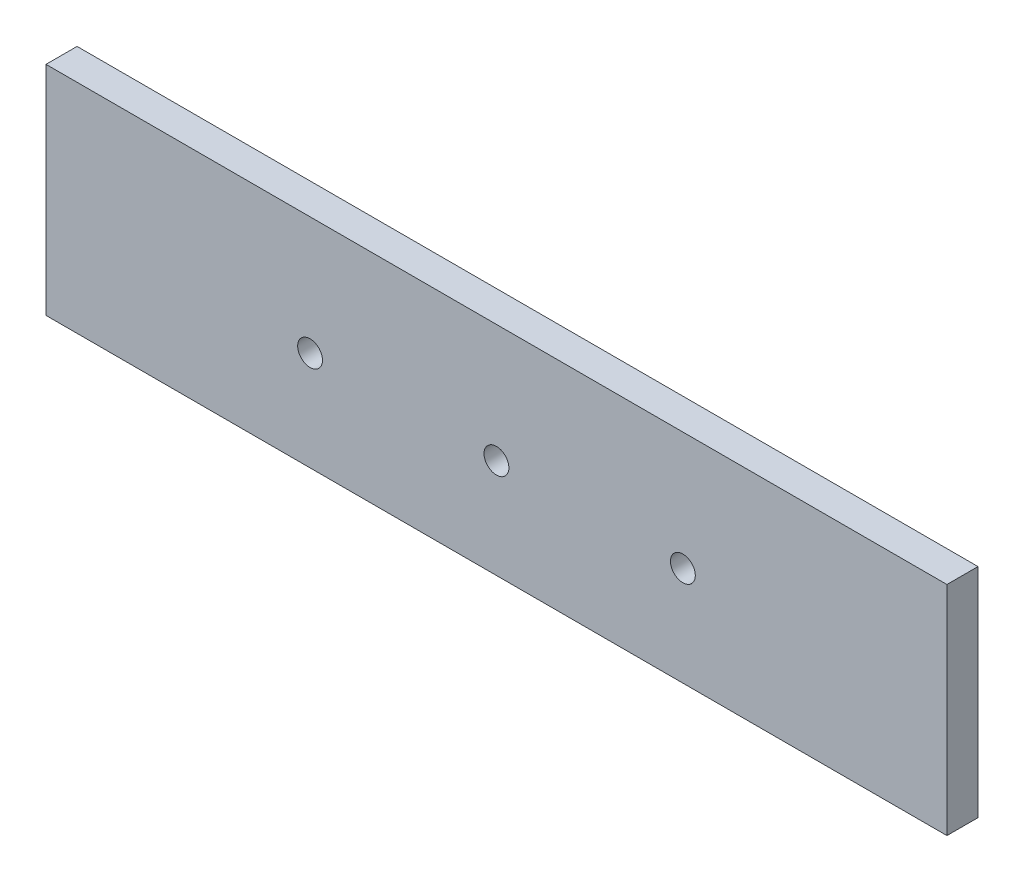
SolidWorks part; units mm, degrees
ref_plane "Front Plane" through (0, 0, 0) normal (0, 0, 1) x (1, 0, 0)
ref_plane "Top Plane" through (0, 0, 0) normal (0, 1, 0) x (1, 0, 0)
ref_plane "Right Plane" through (0, 0, 0) normal (1, 0, 0) x (0, 0, -1)
sketch "Sketch1" plane through (0, 0, 0) normal (0, 0, 1) x (1, 0, 0)
  line L1 (92.075, -22.225) -> (-92.075, -22.225)
  line L2 (92.075, -22.225) -> (92.075, 22.225)
  line L3 (92.075, 22.225) -> (-92.075, 22.225)
  line L4 (-92.075, -22.225) -> (-92.075, 22.225)
  line L5 (92.075, -22.225) -> (-92.075, 22.225) construction
  line L6 (92.075, 22.225) -> (-92.075, -22.225) construction
  point P0 (0, 0)
  dimension "D1" = 184.15
  dimension "D2" = 44.45
extrude "Boss-Extrude1" add sketch "Sketch1" along normal blind 6.35
sketch "Sketch2" plane through (0, 0, 6.35) normal (0, 0, 1) x (1, 0, 0)
  line L0 (-92.075, 22.225) -> (-92.075, -22.225) construction
  line L5 (92.075, -22.225) -> (92.075, 22.225) construction
  line L7 (-92.075, -22.225) -> (92.075, -22.225) construction
  line L9 (57.15, -20.955) -> (-57.15, -20.955)
  line L10 (57.15, -20.955) -> (57.15, 17.145)
  line L11 (57.15, 17.145) -> (-57.15, 17.145)
  line L12 (-57.15, -20.955) -> (-57.15, 17.145)
  line L13 (57.15, -20.955) -> (-57.15, 17.145) construction
  line L14 (57.15, 17.145) -> (-57.15, -20.955) construction
  circle A0 centre (-38.1, -1.905) radius 2.54
  circle A1 centre (0, -1.905) radius 2.54
  circle A2 centre (38.1, -1.905) radius 2.54
  point P0 (0, 0)
  dimension "D4" = 5.08
  dimension "D2" = 38.1
  dimension "D3" = 38.1
  dimension "D5" = 19.05
  dimension "D6" = 38.1
  dimension "D7" = 34.925
  dimension "D8" = 114.3
  dimension "D9" = 34.925
  dimension "D10" = 19.05
  dimension "D11" = 20.32
extrude "Cut-Extrude1" cut sketch "Sketch2" against normal through all contours A0 | A1 | A2
